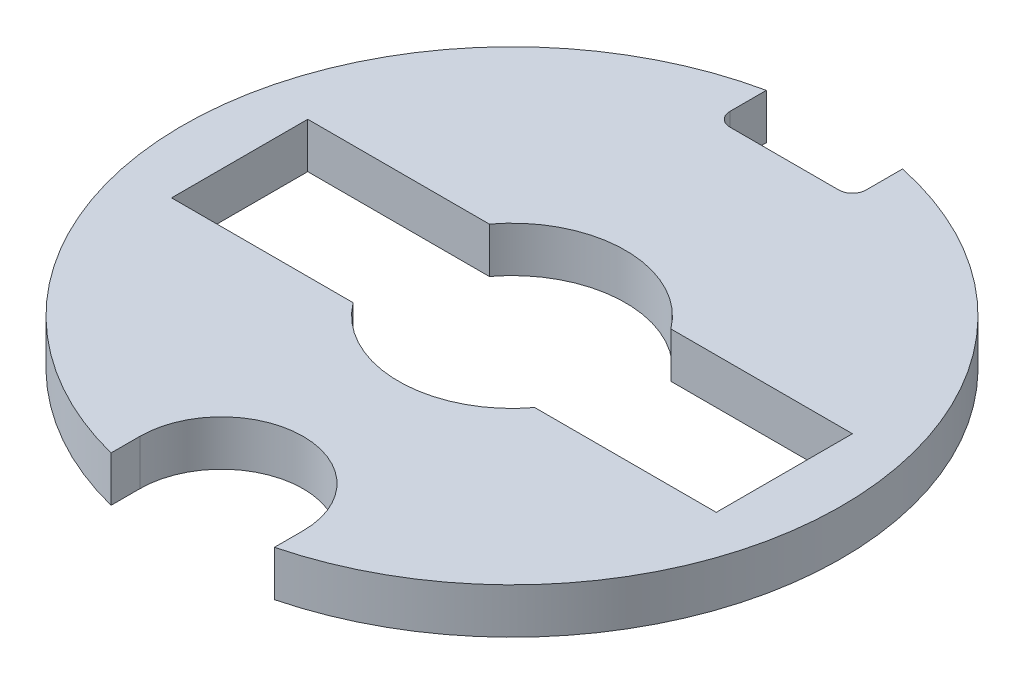
SolidWorks part; units mm, degrees
ref_plane "Front Plane" through (0, 0, 0) normal (0, 0, 1) x (1, 0, 0)
ref_plane "Top Plane" through (0, 0, 0) normal (0, 1, 0) x (1, 0, 0)
ref_plane "Right Plane" through (0, 0, 0) normal (1, 0, 0) x (0, 0, -1)
sketch "Sketch1" plane through (0, 0, 0) normal (0, 1, 0) x (1, 0, 0)
  circle A0 centre (0, 0) radius 7.26
  dimension "D1" = 14.52
extrude "Boss-Extrude1" add sketch "Sketch1" along normal blind 1
sketch "Sketch2" plane through (0, 1, 0) normal (0, 1, 0) x (1, 0, 0)
  line L0 (0, 7.26) -> (0, -7.26) construction
  line L3 (-1.5, 7.1034) -> (-1.5, 6)
  line L4 (-1.5, 6) -> (1.5, 6)
  line L5 (1.5, 7.1034) -> (1.5, 6)
  circle A0 centre (0, 0) radius 7.26 construction
  arc A1 (1.5, 7.1034) -> (-1.5, 7.1034) centre (0, 0) ccw
  dimension "D1" = 3
  dimension "D2" = 6
extrude "Cut-Extrude1" cut sketch "Sketch2" against normal through all
sketch "Sketch3" plane through (0, 1, 0) normal (0, 1, 0) x (1, 0, 0)
  line L0 (2, 1.5) -> (6, 1.5)
  line L1 (-6, -1.5) -> (-2, -1.5)
  line L2 (-6, -1.5) -> (-6, 1.5)
  line L3 (-6, 1.5) -> (-2, 1.5)
  line L4 (6, -1.5) -> (6, 1.5)
  line L5 (-6, -1.5) -> (6, 1.5) construction
  line L6 (-6, 1.5) -> (6, -1.5) construction
  line L7 (2, -1.5) -> (6, -1.5)
  arc A0 (-2, -1.5) -> (2, -1.5) centre (0, 0) ccw
  arc A1 (2, 1.5) -> (-2, 1.5) centre (0, 0) ccw
  point P0 (0, 0)
  dimension "D3" = 2.5
  dimension "D1" = 12
  dimension "D2" = 3
extrude "Cut-Extrude2" cut sketch "Sketch3" against normal through all
sketch "Sketch4" plane through (0, 1, 0) normal (0, 1, 0) x (1, 0, 0)
  line L0 (0, 0) -> (0, -7.26) construction
  line L1 (-1.8, -6.4) -> (-1.8, -7.0333)
  line L2 (1.8, -6.4) -> (1.8, -7.0333)
  arc A0 (-1.5, 7.1034) -> (1.5, 7.1034) centre (0, 0) ccw construction
  arc A1 (1.8, -6.4) -> (-1.8, -6.4) centre (0, -6.4) ccw
  arc A2 (-1.8, -7.0333) -> (1.8, -7.0333) centre (0, 0) ccw
  dimension "D1" = 1.8
  dimension "D2" = 4.6
extrude "Cut-Extrude3" cut sketch "Sketch4" against normal through all
fillet "Fillet1" radius 0.3 2 edges at (1.5, 0.5, -6) (-1.5, 0.5, -6)
